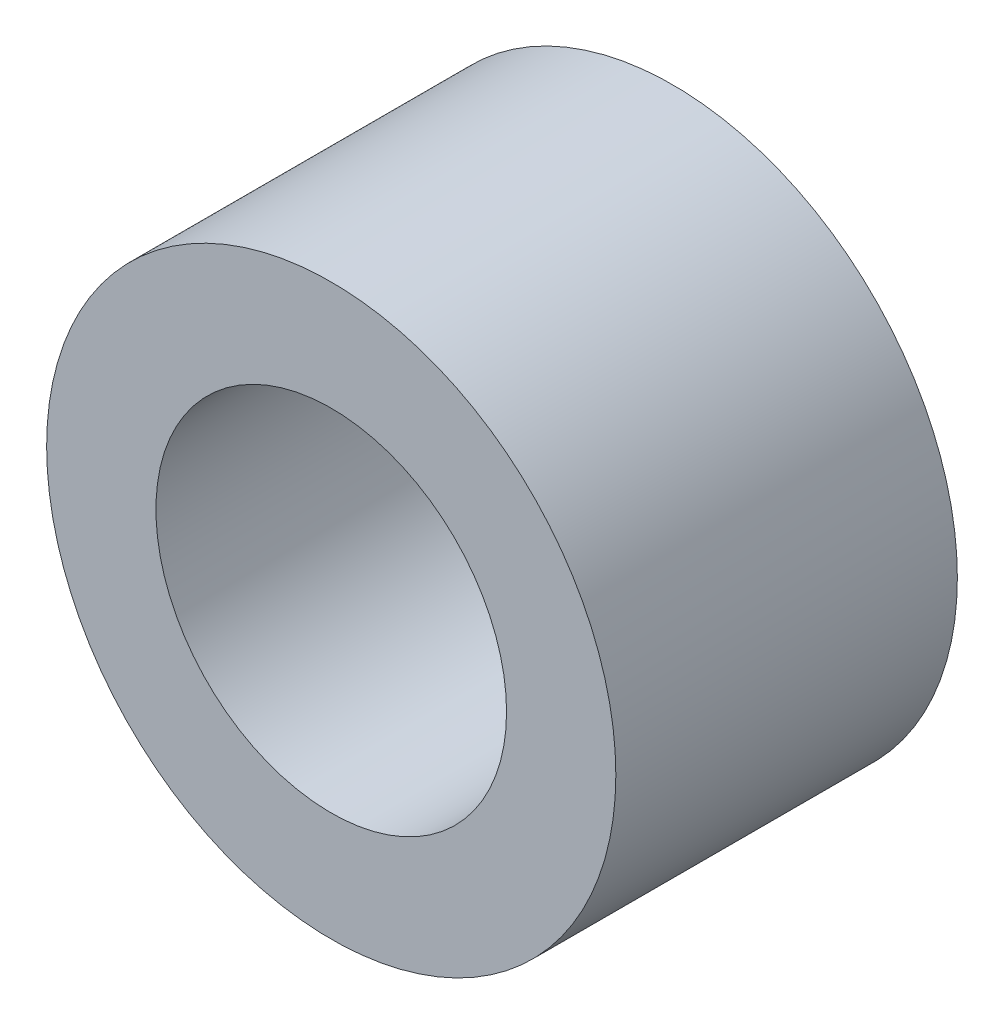
SolidWorks part; units mm, degrees
material "Copper"
ref_plane "Front Plane" through (0, 0, 0) normal (0, 0, 1) x (1, 0, 0)
ref_plane "Top Plane" through (0, 0, 0) normal (0, 1, 0) x (1, 0, 0)
ref_plane "Right Plane" through (0, 0, 0) normal (1, 0, 0) x (0, 0, -1)
sketch "Sketch1" plane through (0, 0, 0) normal (0, 0, 1) x (1, 0, 0)
  circle A0 centre (0, 0) radius 7.9375
  circle A1 centre (0, 0) radius 4.8895
  dimension "D1" = 9.779
  dimension "D2" = 15.875
extrude "Boss-Extrude1" add sketch "Sketch1" along normal blind 9.525
